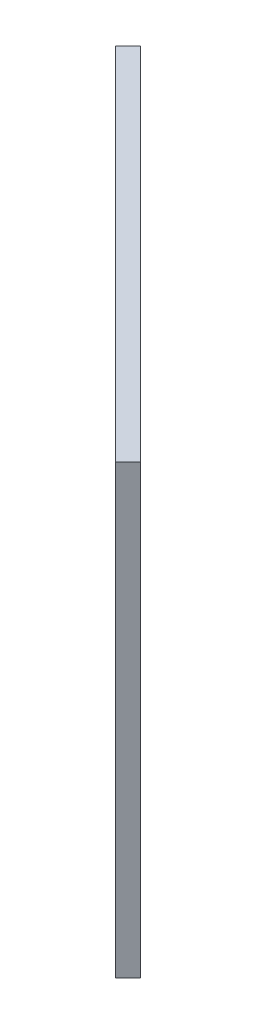
SolidWorks part; units mm, degrees
ref_plane "Front Plane" through (0, 0, 0) normal (0, 0, 1) x (1, 0, 0)
ref_plane "Top Plane" through (0, 0, 0) normal (0, 1, 0) x (1, 0, 0)
ref_plane "Right Plane" through (0, 0, 0) normal (1, 0, 0) x (0, 0, -1)
sketch "Sketch1" plane through (5128.078, 0, -5128.078) normal (0.7071, 0, -0.7071) x (-0.7071, 0, -0.7071)
  line L1 (23153.2706, 40808.2176) -> (23438.2706, 40808.2176)
  line L2 (23153.2706, 40808.2176) -> (23153.2706, 40558.2176)
  line L3 (23153.2706, 40558.2176) -> (23438.2706, 40558.2176)
  line L4 (23438.2706, 40808.2176) -> (23438.2706, 40558.2176)
  line L5 (23153.2706, 40808.2176) -> (23438.2706, 40558.2176) construction
  line L6 (23153.2706, 40558.2176) -> (23438.2706, 40808.2176) construction
  line L7 (23295.7706, 40864.8614) -> (23295.7706, 40809.8614) construction
  point P4 (23295.7706, 40683.2176)
  dimension "D1" = 285
  dimension "D2" = 250
extrude "Boss-Extrude1" add sketch "Sketch1" along normal blind 10
sketch "Sketch2" plane through (5135.1491, 0, -5135.1491) normal (0.7071, 0, -0.7071) x (-0.7071, 0, -0.7071)
  line L0 (23179.8706, 40788.2176) -> (23179.8706, 40674.7176) construction
  line L3 (23183.8706, 40788.2176) -> (23183.8706, 40674.7176)
  line L4 (23175.8706, 40788.2176) -> (23175.8706, 40674.7176)
  line L5 (23354.6706, 40788.2176) -> (23354.6706, 40674.7176) construction
  line L6 (23358.6706, 40788.2176) -> (23358.6706, 40674.7176)
  line L7 (23350.6706, 40788.2176) -> (23350.6706, 40674.7176)
  line L8 (23438.2706, 40558.2176) -> (23438.2706, 40808.2176) construction
  line L9 (23236.8706, 40788.2176) -> (23236.8706, 40674.7176) construction
  line L10 (23240.8706, 40788.2176) -> (23240.8706, 40674.7176)
  line L11 (23232.8706, 40788.2176) -> (23232.8706, 40674.7176)
  line L12 (23411.6706, 40788.2176) -> (23411.6706, 40674.7176) construction
  line L13 (23415.6706, 40788.2176) -> (23415.6706, 40674.7176)
  line L14 (23407.6706, 40788.2176) -> (23407.6706, 40674.7176)
  line L15 (23275.7706, 40788.2176) -> (23275.7706, 40688.2176) construction
  line L16 (23277.8706, 40788.2176) -> (23277.8706, 40688.2176)
  line L17 (23273.6706, 40788.2176) -> (23273.6706, 40688.2176)
  line L18 (23153.2706, 40808.2176) -> (23438.2706, 40808.2176) construction
  line L19 (23153.2706, 40808.2176) -> (23153.2706, 40788.2176) construction
  line L20 (23153.2706, 40788.2176) -> (23438.2706, 40788.2176) construction
  line L21 (23438.2706, 40808.2176) -> (23438.2706, 40788.2176) construction
  line L22 (23313.6706, 40788.2176) -> (23313.6706, 40688.2176)
  line L23 (23317.8706, 40788.2176) -> (23317.8706, 40688.2176)
  line L24 (23315.7706, 40788.2176) -> (23315.7706, 40688.2176) construction
  arc A2 (23183.8706, 40788.2176) -> (23175.8706, 40788.2176) centre (23179.8706, 40788.2176) ccw
  arc A3 (23175.8706, 40674.7176) -> (23183.8706, 40674.7176) centre (23179.8706, 40674.7176) ccw
  arc A4 (23358.6706, 40788.2176) -> (23350.6706, 40788.2176) centre (23354.6706, 40788.2176) ccw
  arc A5 (23350.6706, 40674.7176) -> (23358.6706, 40674.7176) centre (23354.6706, 40674.7176) ccw
  arc A6 (23240.8706, 40788.2176) -> (23232.8706, 40788.2176) centre (23236.8706, 40788.2176) ccw
  arc A7 (23232.8706, 40674.7176) -> (23240.8706, 40674.7176) centre (23236.8706, 40674.7176) ccw
  arc A8 (23415.6706, 40788.2176) -> (23407.6706, 40788.2176) centre (23411.6706, 40788.2176) ccw
  arc A9 (23407.6706, 40674.7176) -> (23415.6706, 40674.7176) centre (23411.6706, 40674.7176) ccw
  arc A10 (23277.8706, 40788.2176) -> (23273.6706, 40788.2176) centre (23275.7706, 40788.2176) ccw
  arc A11 (23273.6706, 40688.2176) -> (23277.8706, 40688.2176) centre (23275.7706, 40688.2176) ccw
  arc A12 (23317.8706, 40788.2176) -> (23313.6706, 40788.2176) centre (23315.7706, 40788.2176) ccw
  arc A13 (23313.6706, 40688.2176) -> (23317.8706, 40688.2176) centre (23315.7706, 40688.2176) ccw
  point P2 (23179.8706, 40731.4676)
  point P10 (23354.6706, 40731.4676)
  point P18 (23236.8706, 40731.4676)
  point P23 (23275.7706, 40738.2176)
  point P27 (23411.6706, 40731.4676)
  point P46 (23315.7706, 40738.2176)
  dimension "D1" = 2
  dimension "D2" = 20
  dimension "D3" = 4
  dimension "D5" = 2.1
  dimension "D6" = 113.5
  dimension "D7" = 100
  dimension "D4" = 2
  dimension "D8" = 2
extrude "Cut-Extrude1" cut sketch "Sketch2" against normal through all both and the other way through all
pattern_linear "LPattern1" [suppressed] count 2 spacing 174.5
chamfer "Chamfer1" distance 2 angle 45 24 edges at (-11422.2304, 40731.4676, -21692.5285) (-11419.402, 40792.2176, -21689.7001) (-11419.402, 40670.7176, -21689.7001) (-11416.5736, 40731.4676, -21686.8717) (-11381.9253, 40731.4676, -21652.2234) (-11379.0969, 40792.2176, -21649.395) (-11379.0969, 40670.7176, -21649.395) (-11376.2685, 40731.4676, -21646.5666) (-11353.0754, 40738.2176, -21623.3735) (-11351.5904, 40790.3176, -21621.8886) (-11351.5904, 40686.1176, -21621.8886) (-11350.1055, 40738.2176, -21620.4036) (-11324.7911, 40738.2176, -21595.0892) (-11323.3062, 40790.3176, -21593.6043) (-11323.3062, 40686.1176, -21593.6043) (-11321.8212, 40738.2176, -21592.1194) (-11298.6281, 40731.4676, -21568.9263) (-11295.7997, 40792.2176, -21566.0978) (-11295.7997, 40670.7176, -21566.0978) (-11292.9713, 40731.4676, -21563.2694) (-11258.3231, 40731.4676, -21528.6212) (-11255.4946, 40792.2176, -21525.7927) (-11255.4946, 40670.7176, -21525.7927) (-11252.6662, 40731.4676, -21522.9643)
sketch "Sketch6" plane through (5135.1491, 0, -5135.1491) normal (0.7071, 0, -0.7071) x (-0.7071, 0, -0.7071)
  line L0 (23375.0473, 40623.4668) -> (23225.0473, 40623.4668) construction
  line L1 (23375.0473, 40620.1168) -> (23225.0473, 40620.1168)
  line L2 (23375.0473, 40626.8168) -> (23225.0473, 40626.8168)
  line L3 (23280.0473, 40626.8168) -> (23320.0473, 40620.1168) construction
  line L4 (23320.0473, 40620.1168) -> (23320.0473, 40626.8168) construction
  line L5 (23320.0473, 40626.8168) -> (23280.0473, 40620.1168) construction
  line L6 (23280.0473, 40620.1168) -> (23280.0473, 40626.8168) construction
  arc A0 (23375.0473, 40620.1168) -> (23375.0473, 40626.8168) centre (23375.0473, 40623.4668) ccw
  arc A1 (23225.0473, 40626.8168) -> (23225.0473, 40620.1168) centre (23225.0473, 40623.4668) ccw
  arc A4 (23375.0473, 40620.1168) -> (23375.0473, 40626.8168) centre (23375.0473, 40623.4668) ccw construction
  arc A5 (23225.0473, 40626.8168) -> (23225.0473, 40620.1168) centre (23225.0473, 40623.4668) ccw construction
  circle A6 centre (23320.0473, 40623.4668) radius 3.35
  circle A7 centre (23280.0473, 40623.4668) radius 3.35
  point P2 (23300.0473, 40623.4668)
  dimension "D1" = 40
extrude "Cut-Extrude4" cut sketch "Sketch6" against normal through all contours A6 | A7
